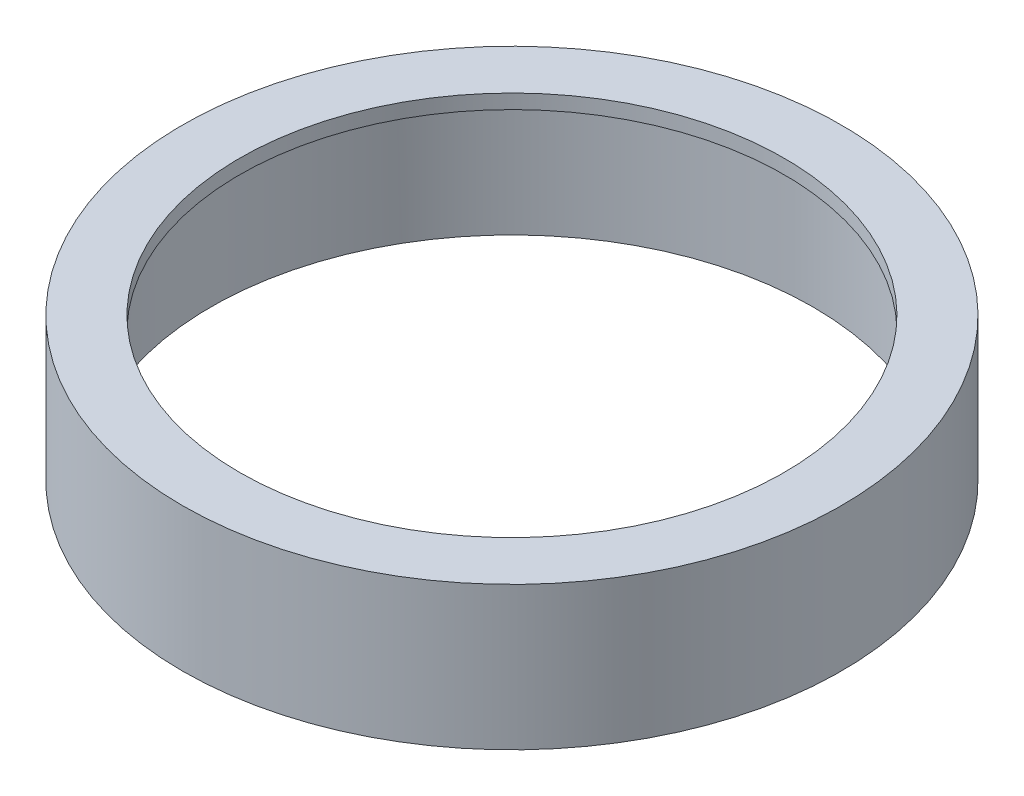
SolidWorks part; units mm, degrees
ref_plane "Front Plane" through (0, 0, 0) normal (0, 0, 1) x (1, 0, 0)
ref_plane "Top Plane" through (0, 0, 0) normal (0, 1, 0) x (1, 0, 0)
ref_plane "Right Plane" through (0, 0, 0) normal (1, 0, 0) x (0, 0, -1)
sketch "Sketch1" plane through (0, 0, 0) normal (0, 1, 0) x (1, 0, 0)
  circle A0 centre (0, 0) radius 115
  circle A1 centre (0, 0) radius 105.05
  dimension "D1" = 230
  dimension "D2" = 210.1
extrude "Boss-Extrude1" add sketch "Sketch1" along normal blind 50
sketch "Sketch2" plane through (0, 50, 0) normal (0, 1, 0) x (1, 0, 0)
  circle A0 centre (0, 0) radius 105.05
  circle A1 centre (0, 0) radius 95
  circle A2 centre (0, 0) radius 105.05 construction
  dimension "D1" = 190
extrude "Boss-Extrude2" add sketch "Sketch2" against normal blind 5
sketch "Sketch3" plane through (0, 45, 0) normal (0, -1, 0) x (1, 0, 0)
  circle A0 centre (0, 0) radius 105.05
  circle A1 centre (0, 0) radius 101.75
  circle A2 centre (0, 0) radius 105.05 construction
  dimension "D1" = 203.5
extrude "Cut-Extrude1" cut sketch "Sketch3" against normal blind 3
sketch "Sketch6" plane through (0, 0, 0) normal (0, 0, 1) x (1, 0, 0)
  line L0 (0, 0) -> (0, 45)
  line L1 (0, 45) -> (95, 45)
  line L2 (95, 45) -> (95, 48)
  line L3 (95, 45) -> (102, 45)
  line L4 (102, 45) -> (102, 48)
  line L5 (102, 48) -> (97, 45)
  dimension "D1" = 95
  dimension "D2" = 102
  dimension "D3" = 3
  dimension "D4" = 5
ref_axis "Axis1" through (0, 48, 0) along (0, -1, 0)
revolve "Cut-Revolve1" cut sketch "Sketch6" angle 360 about axis through (0, 48, 0) along (0, -1, 0)
